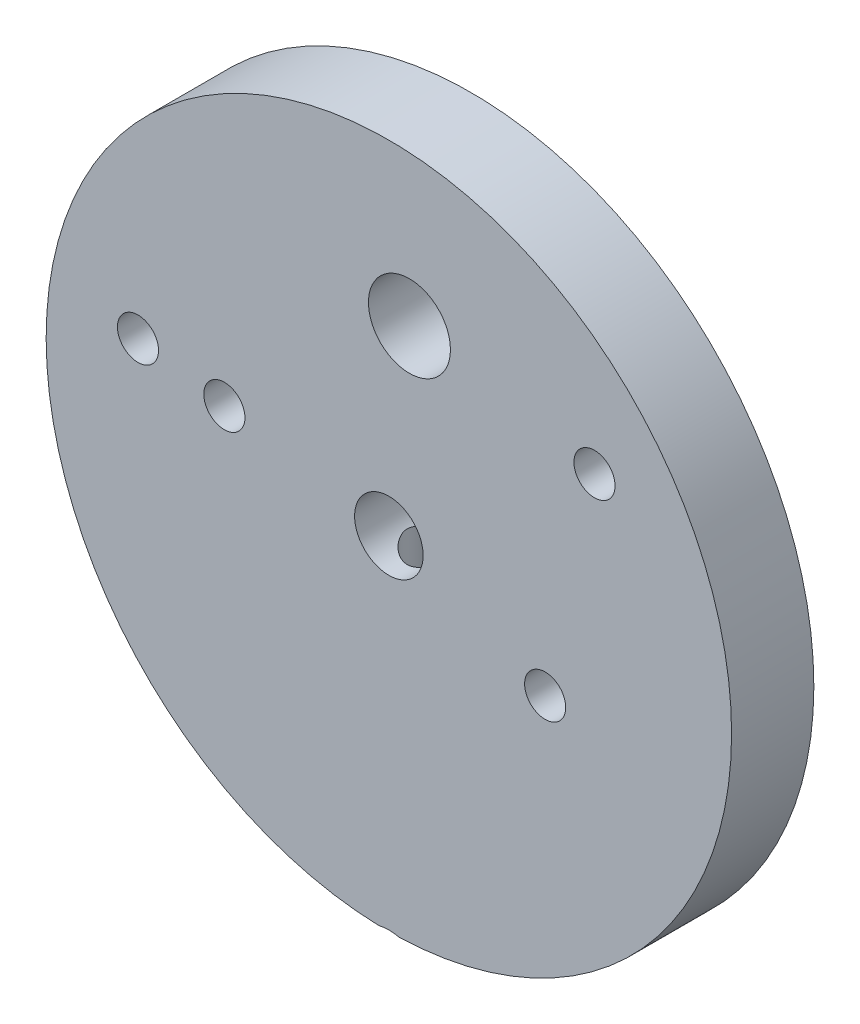
SolidWorks part; units mm, degrees
ref_plane "Plan de face" through (0, 0, 0) normal (0, 0, 1) x (1, 0, 0)
ref_plane "Plan de dessus" through (0, 0, 0) normal (0, 1, 0) x (1, 0, 0)
ref_plane "Plan de droite" through (0, 0, 0) normal (1, 0, 0) x (0, 0, -1)
sketch "Esquisse1" plane through (0, 0, 0) normal (0, 0, 1) x (1, 0, 0)
  circle A0 centre (0, 0) radius 25
  circle A1 centre (-18.3, 3.3) radius 1.5
  circle A2 centre (-12, 2.2) radius 1.5
  circle A3 centre (1.5, 14) radius 2.99
  circle A4 centre (0, 0) radius 2.5
  circle A5 centre (15, 11.4) radius 1.5
  circle A6 centre (11.4, -4.4) radius 1.5
  dimension "D1" = 3
  dimension "D2" = 5
  dimension "D3" = 5.98
  dimension "D4" = 50
  dimension "D5" = 2.2
  dimension "D6" = 12
  dimension "D7" = 3
  dimension "D8" = 18.3
  dimension "D9" = 3.3
  dimension "D10" = 14
  dimension "D12" = 11.4
  dimension "D13" = 15
  dimension "D14" = 11.4
  dimension "D15" = 4.4
  dimension "D11" = 1.5
extrude "Extrusion1" add sketch "Esquisse1" along normal mid plane 6
sketch "Esquisse2" plane through (0, 0, 0) normal (0, 0, 1) x (1, 0, 0)
  line L0 (0, -7.5) -> (0, -25)
  line L1 (0, -25) -> (-3.1, -25)
  line L2 (0, -7.5) -> (0, 0) construction
  line L3 (-3.1, -25) -> (-2.1, -24)
  line L4 (-2.1, -24) -> (-2.1, -7.5)
  line L5 (-2.1, -7.5) -> (0, -7.5)
  line L6 (0, -25) -> (0, -49.8745) construction
  circle A0 centre (0, 0) radius 25 construction
  circle A1 centre (0, 0) radius 25 construction
  dimension "D1" = 4.2
  dimension "D2" = 17.5
  dimension "D3" = 45
  dimension "D4" = 1
revolve "Enlèvement de matière-Révolution1" cut sketch "Esquisse2" angle 360 about L0
hole_wizard "Trou taraudé M4x0.71" positions "Esquisse3D1" profile "Esquisse3" tap size "M4x0.7" standard "ISO"
sketch3d "Esquisse3D1"
  circle A0 centre (0, -7.5, 0) radius 2.1 construction
  point P0 (0, -7.5, 0)
  point P6 (0, -5.4, 0)
sketch "Esquisse3" plane through (0, -7.5, 0) normal (1, 0, 0) x (0, 0, -1)
  line L0 (0, 0) -> (0, 8.4914)
  line L1 (0, 8.4914) -> (1.65, 7.5)
  line L2 (1.65, 7.5) -> (1.65, 0)
  line L5 (1.65, 0) -> (0, 0)
  line L10 (0, 8.4914) -> (-1.65, 7.5) construction
  line L11 (0, -6.35) -> (0, 107.95) construction
  dimension "Diamètre du trou pour taraudage" = 3.3
  dimension "Profondeur du trou pour taraudage" = 7.5
  dimension "Angle de pointe" = 118
cosmetic thread "Filetage de perçage1" parameters "D1"=5.6218, "D2"=4
